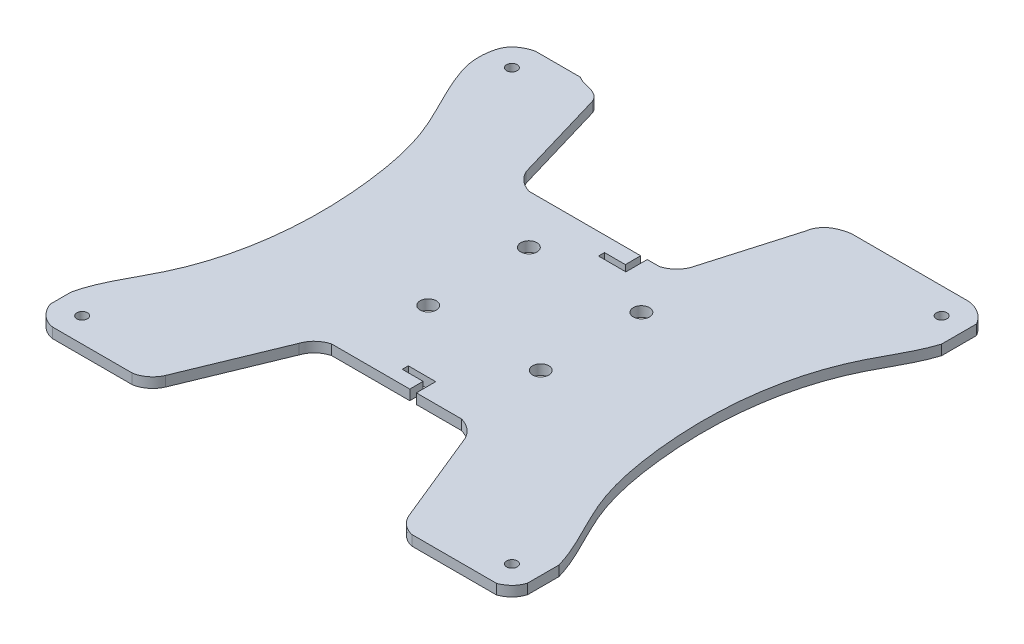
SolidWorks part; units mm, degrees
ref_plane "Front Plane" through (0, 0, 0) normal (0, 0, 1) x (1, 0, 0)
ref_plane "Top Plane" through (0, 0, 0) normal (0, 1, 0) x (1, 0, 0)
ref_plane "Right Plane" through (0, 0, 0) normal (1, 0, 0) x (0, 0, -1)
sketch "Sketch1" plane through (0, 0, 0) normal (0, 1, 0) x (1, 0, 0)
  line L1 (115823.9459, 6663.6753) -> (305823.9459, 6663.6753)
  line L2 (115823.9459, 6663.6753) -> (115823.9459, -183336.3247)
  line L3 (115823.9459, -183336.3247) -> (305823.9459, -183336.3247)
  line L4 (305823.9459, 6663.6753) -> (305823.9459, -183336.3247)
  dimension "D1" = 190000
  dimension "D2" = 190000
extrude "Boss-Extrude1" add sketch "Sketch1" along normal blind 4000
sketch "Sketch3" plane through (0, 4000, 0) normal (0, 1, 0) x (1, 0, 0)
  circle A0 centre (126143.8669, -173624.1497) radius 2100
  circle A1 centre (126143.8669, -3634.077) radius 2100
  circle A2 centre (296154.5427, -3634.077) radius 2100
  circle A3 centre (296154.5427, -173624.1497) radius 2100
  circle A4 centre (191044.6446, -101637.2627) radius 3200
  circle A5 centre (235550.3747, -101637.2627) radius 3200
  circle A6 centre (235550.3747, -61824.2612) radius 3200
  circle A7 centre (191044.6446, -61824.2612) radius 3200
extrude "Cut-Extrude1" cut sketch "Sketch3" against normal blind 5000
sketch "Sketch5" plane through (0, 4000, 0) normal (0, 1, 0) x (1, 0, 0)
  line L0 (207788.9996, -48654.1163) -> (216043.4556, -48654.1163)
  line L1 (207788.9996, -51043.0028) -> (218645.6355, -51043.0028)
  line L2 (207788.9996, -51043.0028) -> (207788.9996, -48654.1163)
  line L4 (218645.6355, -51043.0028) -> (218645.6355, -48654.1163)
  line L6 (216043.4556, -48654.1163) -> (216043.4556, -37602.6209)
  line L7 (216043.4556, -37602.6209) -> (218645.6355, -37602.6209)
  line L8 (218645.6355, -48654.1163) -> (218645.6355, -37602.6209)
  line L9 (207788.9996, -126263.4729) -> (218645.6355, -126263.4729)
  line L10 (207788.9996, -126263.4729) -> (207788.9996, -128654.5662)
  line L12 (218645.6355, -126263.4729) -> (218645.6355, -128654.5662)
  line L14 (218645.6355, -128654.5662) -> (218645.6355, -138374.5349)
  line L15 (218645.6355, -138374.5349) -> (216043.4556, -138374.5349)
  line L16 (216043.4556, -128654.5662) -> (216043.4556, -138374.5349)
  line L17 (207788.9996, -128654.5662) -> (216043.4556, -128654.5662)
extrude "Cut-Extrude2" cut sketch "Sketch5" against normal blind 5000
sketch "Sketch6" plane through (0, 4000, 0) normal (0, 1, 0) x (1, 0, 0)
  line L10 (115823.9459, -183336.3247) -> (305823.9459, -183336.3247) construction
  line L11 (178471.8202, -140109.3598) -> (163071.1706, -177534.5647)
  line L12 (185102.44, -133936.0241) -> (236550.4621, -133936.0241)
  line L13 (243966.1306, -140109.3598) -> (259266.0784, -177534.5647)
  line L14 (266262.4114, -183336.3247) -> (155657.5154, -183336.3247)
  spline S0 degree 3 poles (155657.5154, -183336.3247) (157731.8854, -183020.9942) (160748.7601, -181405.0753) (162605.9075, -178647.3179) (163071.1706, -177534.5647) knots 0 0 0 0 0.634469 1 1 1 1
  spline S1 degree 2 poles (178471.8202, -140109.3598) (180186.6356, -135422.1975) (185102.44, -133936.0241) knots 0 0 0 1 1 1
  spline S2 degree 2 poles (236550.4621, -133936.0241) (241651.0516, -135449.0123) (243966.1306, -140109.3598) knots 0 0 0 1 1 1
  spline S3 degree 3 poles (259266.0784, -177534.5647) (260561.8729, -180397.7518) (263152.5895, -182680.1858) (266262.4114, -183336.3247) knots 0 0 0 0 1 1 1 1
sketch "Sketch8" plane through (0, 4000, 0) normal (0, 1, 0) x (1, 0, 0)
  line L0 (305823.9459, 6663.6753) -> (115823.9459, 6663.6753) construction
  line L11 (230043.2915, -36422.5194) -> (240185.7302, -1546.0396)
  line L12 (223412.6717, -42595.8551) -> (171964.6495, -42595.8551)
  line L13 (164548.9811, -36422.5194) -> (153591.4478, 716.2594)
  line L14 (140636.0358, 10985.9106) -> (250330.1314, 6663.6753)
  spline S0 degree 3 poles (240185.7302, -1546.0396) (240437.5203, 680.2783) (241984.6214, 3139.2808) (246534.9345, 6145.656) (249963.2413, 6629.2002) (250330.1314, 6663.6753) knots 0 0 0 0 0.397895 0.502774 1 1 1 1
  spline S1 degree 2 poles (230043.2915, -36422.5194) (228328.476, -41109.6817) (223412.6717, -42595.8551) knots 0 0 0 1 1 1
  spline S2 degree 2 poles (171964.6495, -42595.8551) (166864.06, -41082.8669) (164548.9811, -36422.5194) knots 0 0 0 1 1 1
  spline S3 degree 3 poles (153591.4478, 716.2594) (151101.7422, 7156.1194) (141822.0652, 2701.6681) (140636.0358, 10985.9106) knots 0 0 0 0 1 1 1 1
  point P1 (153591.4478, 716.2594)
  point P8 (150462.1508, 3978.9674)
  point P9 (0, 0)
  point P14 (252421.6888, 7303.4437)
  point P18 (244770.5216, 4925.8614)
  point P20 (252600.4544, 6972.7274)
  point P21 (250330.1314, 6663.6753)
  point P24 (140636.0358, 10985.9106)
extrude "Cut-Extrude3" cut sketch "Sketch6" against normal blind 5000
extrude "Cut-Extrude5" cut sketch "Sketch8" against normal blind 5000
sketch "Sketch10" plane through (0, 4000, 0) normal (0, 1, 0) x (1, 0, 0)
  line L0 (142979.7482, 6663.6753) -> (115823.9459, 6663.6753) construction
  line L1 (115823.9459, 6663.6753) -> (115823.9459, -183336.3247) construction
  line L2 (115823.9459, -183336.3247) -> (155657.5154, -183336.3247) construction
  line L3 (126568.265, -183336.3247) -> (126568.265, -185665.6094)
  line L4 (126568.265, -185665.6094) -> (109180.2345, -185665.6094)
  line L5 (109180.2345, -185665.6094) -> (109180.2345, 6663.6753)
  line L6 (109180.2345, 6663.6753) -> (125030.1869, 6663.6753)
  spline S0 degree 3 poles (125030.1869, 6663.6753) (122562.2241, 5997.7958) (117653.0797, 3615.3751) (115804.2754, -3836.4506) (115954.6531, -10247.0772) (120119.8748, -23556.5735) (131610.5892, -41750.3039) (136879.2969, -68571.1063) (138850.7071, -102510.8622) (132793.2247, -136861.2938) (117762.3165, -158664.1403) (115823.9459, -167788.0981) knots 0 0 0 0 0.043041 0.07798 0.116648 0.146192 0.301252 0.459464 0.579595 0.851432 1 1 1 1
  spline S1 degree 3 poles (115823.9459, -167788.0981) (112994.7905, -174724.143) (118558.0514, -184380.4128) (126568.265, -183336.3247) knots 0 0 0 0 1 1 1 1
sketch "Sketch12" plane through (0, 4000, 0) normal (0, 1, 0) x (1, 0, 0)
  line L3 (296051.1743, 6663.6753) -> (296051.1743, 8218.8565)
  line L4 (296051.1743, 8218.8565) -> (313439.2048, 8218.8565)
  line L5 (313439.2048, 8218.8565) -> (313439.2048, -184110.4282)
  line L6 (313439.2048, -184110.4282) -> (297589.2524, -184110.4282)
  line L7 (305823.9459, 6663.6753) -> (250330.1314, 6663.6753) construction
  spline S0 degree 3 poles (297589.2524, -184110.4282) (300057.2152, -183444.5487) (304966.3596, -181062.128) (306815.1639, -173610.3023) (306664.7863, -167199.6757) (302499.5645, -153890.1794) (291008.8502, -135696.449) (285740.1424, -108875.6466) (283768.7323, -74935.8906) (289826.2146, -40585.4591) (304857.1228, -18782.6126) (306795.4934, -9658.6548) knots 0 0 0 0 0.043041 0.07798 0.116648 0.146192 0.301252 0.459464 0.579595 0.851432 1 1 1 1
  spline S1 degree 3 poles (306795.4934, -9658.6548) (309763.1738, -2284.483) (303711.4241, 6332.7875) (296051.1743, 6663.6753) knots 0 0 0 0 1 1 1 1
  point P2 (296051.1743, 6663.6753)
extrude "Cut-Extrude6" cut sketch "Sketch10" against normal blind 5000
extrude "Cut-Extrude7" cut sketch "Sketch12" against normal blind 5000
